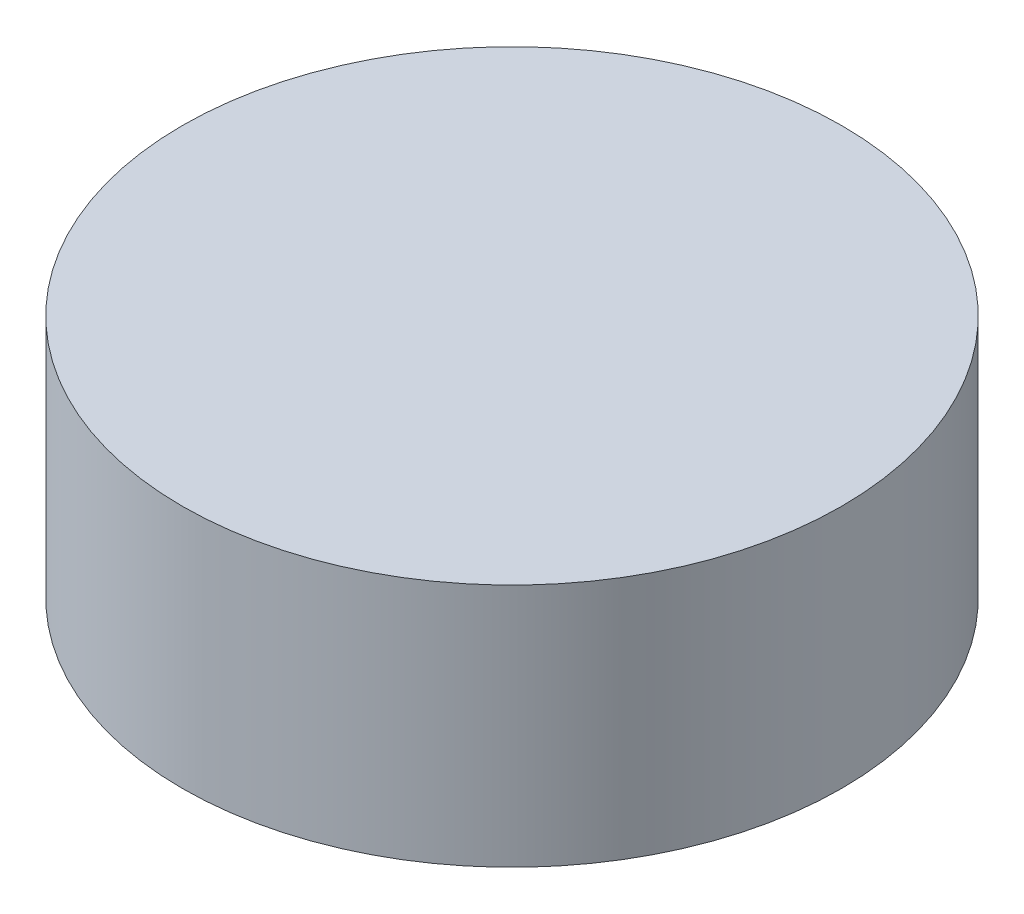
SolidWorks part; units mm, degrees
material "Epoxy, Unfilled"
ref_plane "Front Plane" through (0, 0, 0) normal (0, 0, 1) x (1, 0, 0)
ref_plane "Top Plane" through (0, 0, 0) normal (0, 1, 0) x (1, 0, 0)
ref_plane "Right Plane" through (0, 0, 0) normal (1, 0, 0) x (0, 0, -1)
sketch "Sketch1" plane through (0, 0, 0) normal (0, 1, 0) x (1, 0, 0)
  circle A0 centre (0, 0) radius 13.49
  dimension "D1" = 26.98
extrude "Boss-Extrude1" add sketch "Sketch1" along normal blind 10
